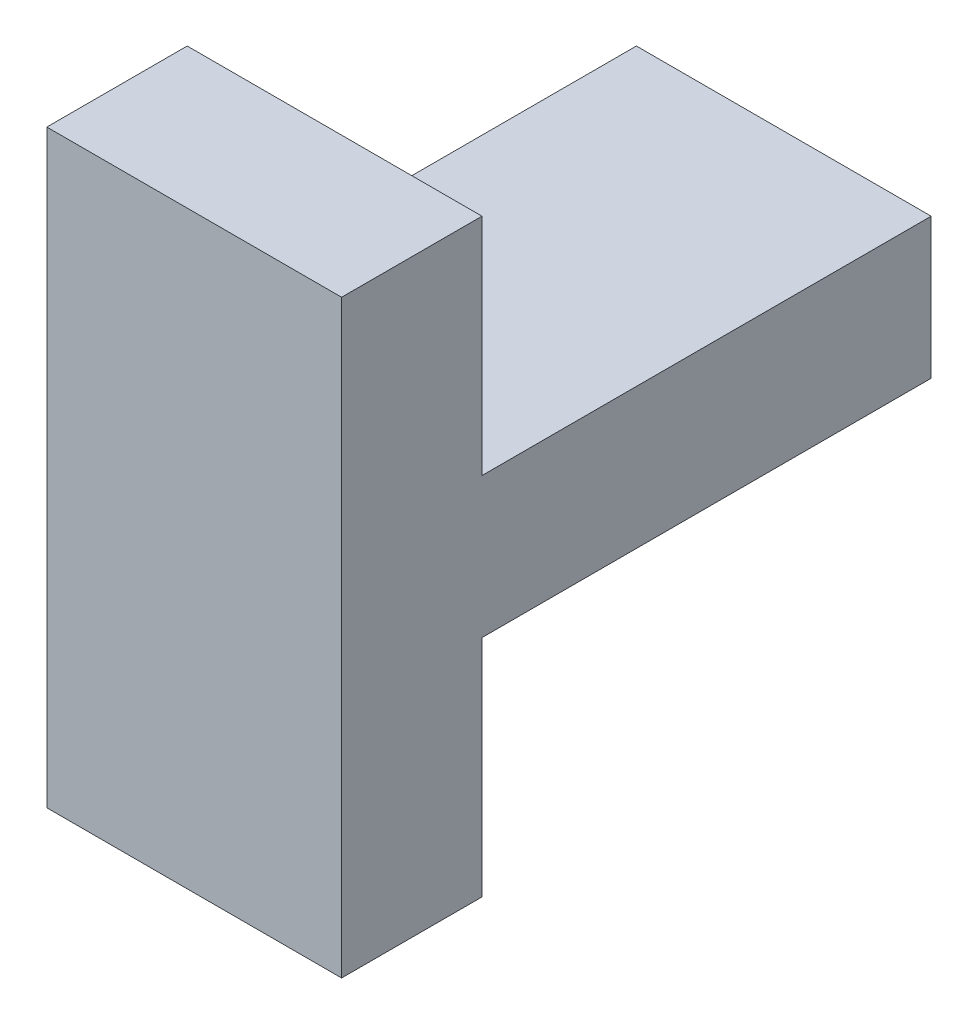
SolidWorks part; units mm, degrees
material "1060 Alloy"
ref_plane "Front Plane" through (0, 0, 0) normal (1, 0, 0) x (0, 1, 0)
ref_plane "Top Plane" through (0, 0, 0) normal (0, 0, 1) x (0, 1, 0)
ref_plane "Right Plane" through (0, 0, 0) normal (0, 1, 0) x (-1, 0, 0)
sketch "Sketch1" plane through (0, 0, 0) normal (1, 0, 0) x (0, 1, 0)
  line L0 (0, 0) -> (10, 0)
  line L1 (10, 0) -> (10, 32)
  line L2 (10, 32) -> (26, 32)
  line L3 (26, 32) -> (26, 42)
  line L4 (26, 42) -> (-16, 42)
  line L5 (-16, 42) -> (-16, 32)
  line L6 (-16, 32) -> (0, 32)
  line L7 (0, 32) -> (0, 0)
  dimension "D1" = 10
  dimension "D2" = 32
  dimension "D3" = 16
  dimension "D4" = 10
  dimension "D5" = 42
extrude "Boss-Extrude1" add sketch "Sketch1" along normal blind 21
